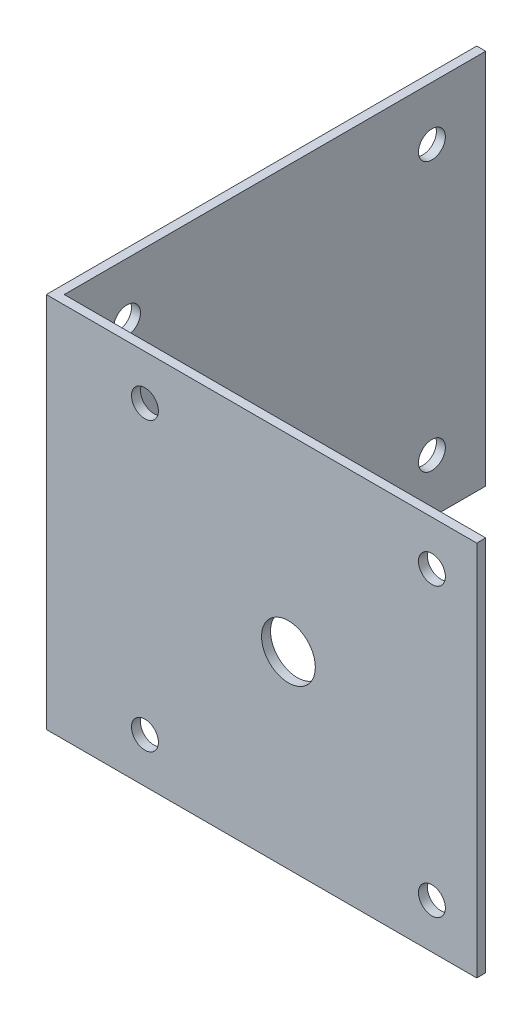
SolidWorks part; units mm, degrees
ref_plane "Front Plane" through (0, 0, 0) normal (0, 0, 1) x (1, 0, 0)
ref_plane "Top Plane" through (0, 0, 0) normal (0, 1, 0) x (1, 0, 0)
ref_plane "Right Plane" through (0, 0, 0) normal (1, 0, 0) x (0, 0, -1)
sketch "Sketch1" plane through (0, 0, 0) normal (0, 1, 0) x (1, 0, 0)
  line L0 (0, 0) -> (0, 48)
  line L1 (0, 0) -> (48, 0)
  line L2 (0, 48) -> (1, 48)
  line L3 (1, 48) -> (1, 1)
  line L4 (1, 1) -> (48, 1)
  line L5 (48, 0) -> (48, 1)
  dimension "D1" = 48
  dimension "D2" = 48
  dimension "D3" = 1
  dimension "D4" = 1
extrude "Boss-Extrude1" add sketch "Sketch1" along normal blind 42
sketch "Sketch2" plane through (0, 0, 0) normal (0, 0, 1) x (1, 0, 0)
  line L0 (55.1575, 37) -> (-11.7747, 37) construction
  line L1 (55.1575, 5) -> (-8.6786, 5) construction
  line L2 (43, 45.1209) -> (43, -3.1784) construction
  line L3 (11, 45.1209) -> (11, -3.1784) construction
  line L4 (48, 42) -> (48, 0) construction
  line L5 (27, 43.4907) -> (27, -3.1784) construction
  line L6 (51.9032, 21) -> (-4.0826, 21) construction
  circle A0 centre (11, 37) radius 1.5
  circle A1 centre (43, 37) radius 1.5
  circle A2 centre (43, 5) radius 1.5
  circle A3 centre (11, 5) radius 1.5
  circle A4 centre (27, 21) radius 3
  dimension "D5" = 3
  dimension "D6" = 3
  dimension "D7" = 3
  dimension "D8" = 3
  dimension "D1" = 5
  dimension "D2" = 11
  dimension "D3" = 5
  dimension "D4" = 5
  dimension "D9" = 21
  dimension "D10" = 21
extrude "Cut-Extrude1" cut sketch "Sketch2" against normal blind 42
sketch "Sketch3" plane through (0, 0, 0) normal (1, 0, 0) x (0, 0, -1)
  line L0 (54.2603, 36) -> (-11.9111, 36) construction
  line L1 (54.2603, 6) -> (-10.8375, 6) construction
  line L2 (42, 44.4547) -> (42, -3.634) construction
  line L3 (8, 44.4547) -> (8, -3.634) construction
  line L4 (1, 42) -> (48, 42) construction
  line L5 (48, 42) -> (48, 0) construction
  line L6 (0, 42) -> (0, 0) construction
  line L7 (1, 0) -> (48, 0) construction
  circle A0 centre (42, 36) radius 1.5
  circle A1 centre (42, 6) radius 1.5
  circle A2 centre (8, 6) radius 1.5
  circle A3 centre (8, 36) radius 1.5
  dimension "D5" = 3
  dimension "D6" = 3
  dimension "D7" = 3
  dimension "D8" = 3
  dimension "D1" = 6
  dimension "D2" = 6
  dimension "D3" = 8
  dimension "D4" = 6
extrude "Cut-Extrude2" cut sketch "Sketch3" along normal blind 42
